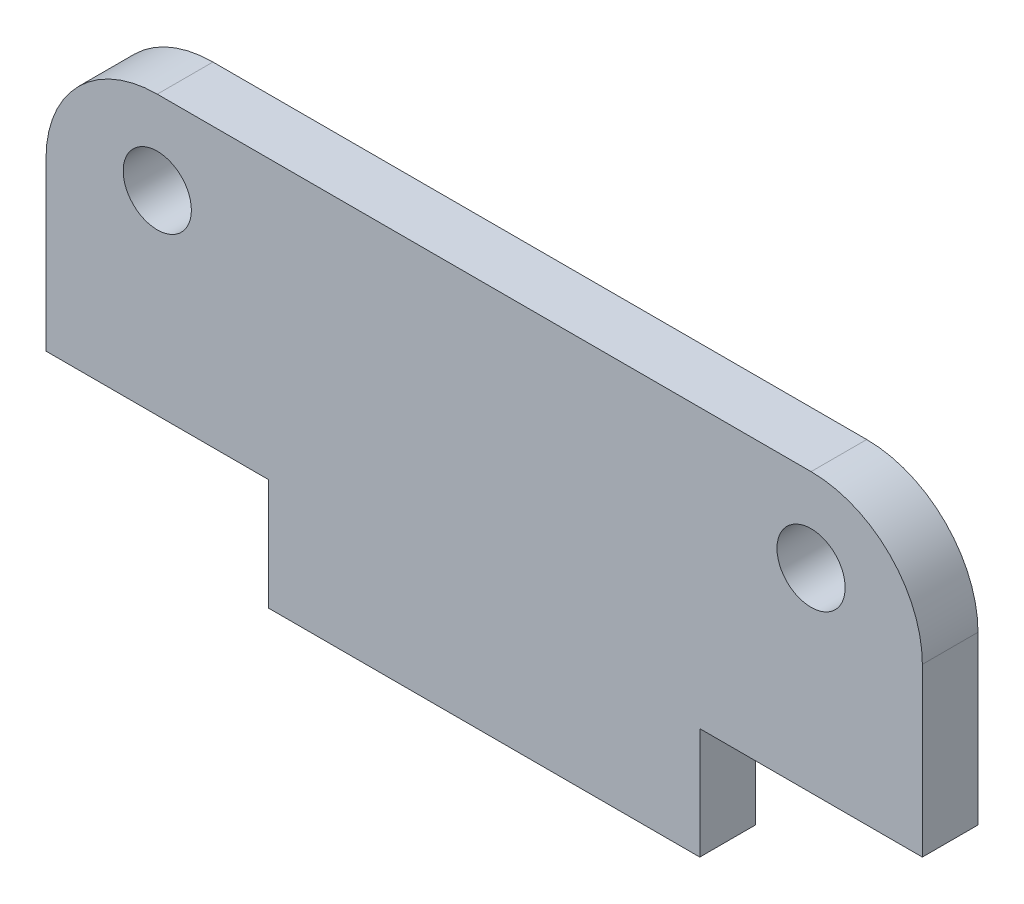
SolidWorks part; units mm, degrees
material "ABS"
ref_plane "Front Plane" through (0, 0, 0) normal (0, 0, 1) x (1, 0, 0)
ref_plane "Top Plane" through (0, 0, 0) normal (0, 1, 0) x (1, 0, 0)
ref_plane "Right Plane" through (0, 0, 0) normal (1, 0, 0) x (0, 0, -1)
sketch "Sketch1" plane through (0, 0, 0) normal (0, 0, 1) x (1, 0, 0)
  line L0 (-15.75, -7) -> (-7.75, -7)
  line L1 (-11.75, 3) -> (11.75, 3)
  line L2 (-15.75, -1) -> (-15.75, -7)
  line L3 (-7.75, -11) -> (7.75, -11)
  line L4 (7.75, -11) -> (7.75, -7)
  line L5 (15.75, -1) -> (15.75, -7)
  line L6 (-7.75, -11) -> (-7.75, -7)
  line L7 (0, 3) -> (0, -11) construction
  line L8 (15.75, -7) -> (7.75, -7)
  circle A0 centre (-11.75, 0) radius 1.225
  arc A1 (11.75, 3) -> (15.75, -1) centre (11.75, -1) cw
  circle A2 centre (11.75, 0) radius 1.225
  arc A3 (-11.75, 3) -> (-15.75, -1) centre (-11.75, -1) ccw
  dimension "D1" = 2.45
  dimension "D3" = 4
  dimension "D2" = 11.75
  dimension "D4" = 1
  dimension "D6" = 7.75
  dimension "D7" = 4
  dimension "D8" = 14
  dimension "D5" = 15.75
extrude "Main Body" add sketch "Sketch1" along normal blind 2
equation "\"D1@Sketch1\"=2.00mm+\"print_free@Parameters@RobotHandParameters.SLDPRT\""
